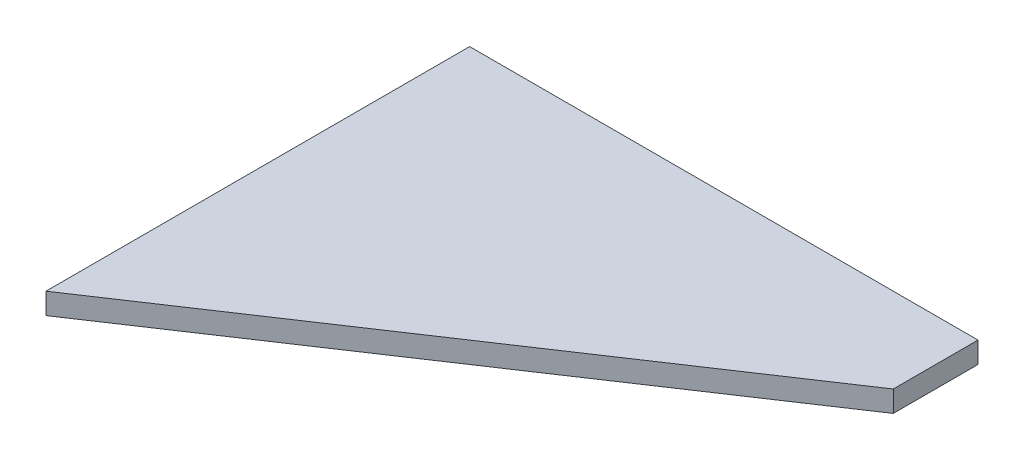
SolidWorks part; units mm, degrees
ref_plane "Front Plane" through (0, 0, 0) normal (0, 0, 1) x (1, 0, 0)
ref_plane "Top Plane" through (0, 0, 0) normal (0, 1, 0) x (1, 0, 0)
ref_plane "Right Plane" through (0, 0, 0) normal (1, 0, 0) x (0, 0, -1)
sketch "Sketch2" plane through (0, 0, 0) normal (0, 1, 0) x (1, 0, 0)
  line L0 (0, 0) -> (0, 63.5)
  line L1 (0, 63.5) -> (76.2, 63.5)
  line L2 (76.2, 63.5) -> (76.2, 50.8)
  line L3 (76.2, 50.8) -> (0, 0)
  point P3 (76.2, 57.15)
  dimension "D1" = 63.5
  dimension "D2" = 12.7
  dimension "D3" = 76.2
extrude "Boss-Extrude2" add sketch "Sketch2" along normal blind 3.175 contours L1 L2 L3 L0
sketch "Sketch4" plane through (0, 0, 0) normal (0, -1, 0) x (1, 0, 0)
  line L0 (0, 0) -> (0, -63.5) construction
  line L1 (0, -42.5976) -> (12.7, -42.5976)
  line L2 (0, -42.5976) -> (0, -49.5246)
  line L3 (0, -49.5246) -> (12.7, -49.5246)
  line L4 (12.7, -42.5976) -> (12.7, -49.5246)
  line L5 (0, 0) -> (0, -63.5) construction
  line L7 (0, -63.5) -> (76.2, -63.5) construction
  line L8 (76.2, -63.5) -> (76.2, -50.8) construction
  point P6 (0, 0)
  point P7 (0, 0)
  point P8 (0, 0)
  point P13 (12.7, -46.0611)
  dimension "D1" = 6.9271
  dimension "D2" = 12.7
  dimension "D3" = 13.9754
  dimension "D4" = 42.5976
  dimension "D5" = 63.5
